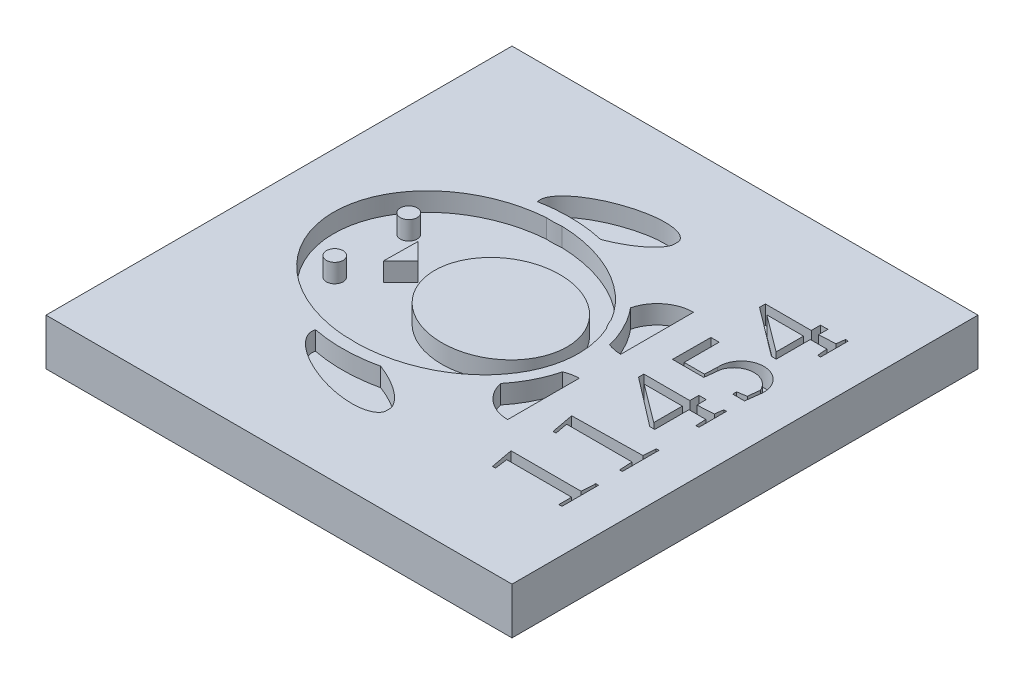
SolidWorks part; units mm, degrees
ref_plane "Front Plane" through (0, 0, 0) normal (0, 0, 1) x (1, 0, 0)
ref_plane "Top Plane" through (0, 0, 0) normal (0, 1, 0) x (1, 0, 0)
ref_plane "Right Plane" through (0, 0, 0) normal (1, 0, 0) x (0, 0, -1)
sketch "Sketch3" plane through (0, 0, 0) normal (0, 1, 0) x (1, 0, 0)
  line L1 (-31.75, 31.75) -> (31.75, 31.75)
  line L2 (-31.75, 31.75) -> (-31.75, -31.75)
  line L3 (-31.75, -31.75) -> (31.75, -31.75)
  line L4 (31.75, 31.75) -> (31.75, -31.75)
  line L5 (-31.75, 31.75) -> (31.75, -31.75) construction
  line L6 (-31.75, -31.75) -> (31.75, 31.75) construction
  point P0 (0, 0)
  dimension "D1" = 63.5
  dimension "D2" = 63.5
extrude "Boss-Extrude1" add sketch "Sketch3" along normal blind 6.35
sketch "Sketch4" plane through (0, 6.35, 0) normal (0, 1, 0) x (1, 0, 0)
  line L0 (-31.75, 0) -> (31.75, 0)
  line L1 (-31.75, 31.75) -> (-31.75, -31.75) construction
  line L2 (31.75, -31.75) -> (31.75, 31.75) construction
  line L3 (0, -31.75) -> (0, 31.75)
  line L4 (-31.75, -31.75) -> (31.75, -31.75) construction
  line L5 (31.75, 31.75) -> (-31.75, 31.75) construction
  line L6 (6.1011, -12.941) -> (6.1011, 12.941)
  line L7 (-11.491, -10.0831) -> (-11.491, 10.0831)
  line L8 (-11.491, 10.0831) -> (-11.491, 0)
  line L9 (-11.491, 0) -> (-11.491, -10.0831)
  line L10 (-11.491, 0) -> (-11.491, 10.0831)
  line L11 (-7.6663, -12.3498) -> (-7.3296, 12.4908)
  line L12 (-7.4679, 2.2902) -> (-5.1777, 0)
  line L13 (-5.1777, 0) -> (-7.5308, -2.3531)
  line L14 (19.6532, 0) -> (19.6532, 15.494)
  line L15 (19.6532, 15.494) -> (19.6532, -15.494)
  line L16 (19.6532, -15.494) -> (19.6532, 0)
  line L17 (19.6532, -15.494) -> (19.6532, 0)
  line L18 (19.6532, 0) -> (19.6532, -15.494)
  line L19 (3.1453, 17.5998) -> (3.1453, 13.6542)
  line L20 (3.1453, -17.5998) -> (3.1453, -13.6542)
  line L21 (10.3047, 20.0808) -> (10.3047, 10.9368)
  line L22 (10.3365, -20.0599) -> (10.3365, -10.9159)
  circle A0 centre (-11.491, -5.0416) radius 1.143
  circle A1 centre (-11.491, 5.0416) radius 1.143
  circle A2 centre (19.6532, 7.747) radius 4.9623
  circle A3 centre (19.6532, -7.747) radius 4.8737
  ellipse E0 centre (0, 0) end of major axis (16.6899, 0) minor radius 13.9033
  ellipse E1 centre (6.1011, 0) end of major axis (15.1321, 0) minor radius 8.0476
  ellipse E2 centre (0, 0) end of major axis (18.157, 0) minor radius 15.5025
  ellipse E3 centre (3.1453, 17.5998) end of major axis (-4.0142, 15.1189) minor radius 3.0241
  ellipse E4 centre (3.1453, -17.5998) end of major axis (10.3365, -20.0599) minor radius 2.9995
  point P51 (3.1453, -17.5998)
  point P60 (10.3365, -20.0599)
  dimension "D1" = 2.286
  dimension "D2" = 2.286
  dimension "D3" = 15.494
  dimension "D4" = 15.494
  dimension "D5" = 3.9457
  dimension "D6" = 9.144
  dimension "D7" = 9.144
  dimension "D8" = 3.9457
extrude "Cut-Extrude1" cut sketch "Sketch4" against normal blind 2.54
sketch "Sketch6" plane through (31.75, 0, 0) normal (1, 0, 0) x (0, 0, -1)
  line L1 (31.75, 6.35) -> (-31.75, 6.35)
  line L2 (31.75, 6.35) -> (31.75, 0)
  line L3 (31.75, 0) -> (-31.75, 0)
  line L4 (-31.75, 6.35) -> (-31.75, 0)
extrude "Boss-Extrude2" add sketch "Sketch6" along normal blind 7.62
sketch "Sketch7" plane through (-31.75, 0, 0) normal (-1, 0, 0) x (0, 0, 1)
  line L1 (-31.75, 0) -> (31.75, 0)
  line L2 (-31.75, 0) -> (-31.75, 6.35)
  line L3 (-31.75, 6.35) -> (31.75, 6.35)
  line L4 (31.75, 0) -> (31.75, 6.35)
extrude "Cut-Extrude2" cut sketch "Sketch7" against normal blind 7.62
sketch "Sketch12" plane through (0, 6.35, 0) normal (0, 1, 0) x (1, 0, 0)
  line L0 (33.5932, -31.75) -> (33.5932, 31.75)
  line L1 (-24.13, -31.75) -> (39.37, -31.75) construction
  line L2 (39.37, 31.75) -> (-24.13, 31.75) construction
  line L5 (33.5932, -19.1511) -> (33.1665, -19.1863)
  line L6 (33.1665, -19.1863) -> (33.1665, -17.423)
  line L7 (33.1665, -17.423) -> (24.3207, -17.423)
  line L8 (24.3207, -17.423) -> (24.5493, -19.1863)
  line L9 (24.5493, -19.1863) -> (24.1456, -19.1863)
  line L10 (24.1456, -19.1863) -> (23.5653, -16.0773)
  line L11 (23.5653, -16.0773) -> (33.1252, -16.0773)
  line L12 (33.1252, -16.0773) -> (33.2261, -14.1817)
  line L13 (33.2261, -14.1817) -> (33.5932, -14.1817)
  line L14 (33.5932, -14.1817) -> (33.5932, -19.1511)
  line L15 (23.5653, -7.8157) -> (24.1456, -10.935)
  line L16 (24.1456, -10.935) -> (24.5493, -10.935)
  line L17 (24.5493, -10.935) -> (24.2174, -9.1511)
  line L18 (24.2174, -9.1511) -> (33.1252, -9.1511)
  line L19 (33.1252, -9.1511) -> (33.2261, -10.935)
  line L20 (33.2261, -10.935) -> (33.5932, -10.935)
  line L21 (33.5932, -10.935) -> (33.5932, -5.9501)
  line L22 (33.5932, -5.9501) -> (33.2261, -5.9501)
  line L23 (33.2261, -5.9501) -> (33.1252, -7.6508)
  line L24 (33.1252, -7.6508) -> (23.5653, -7.8157)
  line L25 (23.5653, 1.2976) -> (30.1596, -3.7688)
  line L26 (30.1596, -3.7688) -> (30.8413, -3.7688)
  line L27 (30.8413, -3.7688) -> (30.8413, 0.8967)
  line L28 (30.8413, 0.8967) -> (33.1252, 0.8967)
  line L29 (33.1252, 0.8967) -> (33.2047, -0.5088)
  line L30 (33.2047, -0.5088) -> (33.5932, -0.5088)
  line L31 (33.5932, -0.5088) -> (33.5932, 3.2621)
  line L32 (33.5932, 3.2621) -> (33.2261, 3.2621)
  line L33 (33.2261, 3.2621) -> (33.0711, 2.1132)
  line L34 (33.0711, 2.1132) -> (30.8413, 1.987)
  line L35 (30.8413, 1.987) -> (30.8193, 3.2621)
  line L36 (30.8193, 3.2621) -> (29.8201, 3.2621)
  line L37 (29.8201, 3.2621) -> (29.8201, 2.028)
  line L38 (29.8201, 2.028) -> (23.5653, 2.028)
  line L39 (23.5653, 2.028) -> (23.5653, 1.2976)
  line L40 (24.5493, 0.8967) -> (29.8201, -3.1529)
  line L41 (29.8201, -3.1529) -> (29.8201, 0.8967)
  line L42 (24.5493, 0.8967) -> (29.8201, 0.8967)
  line L43 (33.872, 7.8761) -> (33.5932, 5.7123)
  line L44 (33.5932, 5.7123) -> (31.9822, 5.7123)
  line L45 (31.9822, 5.7123) -> (31.9822, 6.2447)
  line L46 (31.9822, 6.2447) -> (33.2261, 6.4512)
  line L47 (33.2261, 6.4512) -> (33.4138, 8.0633)
  line L48 (28.2811, 7.8007) -> (28.0379, 5.7123)
  line L49 (28.0379, 5.7123) -> (23.7767, 5.7123)
  line L50 (23.7767, 5.7123) -> (23.8069, 10.9197)
  line L51 (23.8069, 10.9197) -> (24.9322, 10.9197)
  line L52 (24.9322, 10.9197) -> (24.9322, 6.1458)
  line L53 (24.9322, 6.1458) -> (27.6984, 6.1458)
  line L54 (27.6984, 6.1458) -> (27.7736, 7.8761)
  line L55 (33.5932, 16.074) -> (33.5932, 19.8467)
  line L56 (33.5932, 19.8467) -> (33.2261, 19.8467)
  line L57 (33.2261, 19.8467) -> (33.0775, 18.6928)
  line L58 (33.0775, 18.6928) -> (30.8228, 18.5789)
  line L59 (30.8228, 18.5789) -> (30.8228, 19.8467)
  line L60 (30.8228, 19.8467) -> (29.8201, 19.8295)
  line L61 (29.8201, 19.8295) -> (29.8201, 18.5789)
  line L62 (29.8201, 18.5789) -> (23.5653, 18.5789)
  line L63 (23.5653, 18.5789) -> (23.5653, 17.7846)
  line L64 (23.5653, 17.7846) -> (30.1596, 12.808)
  line L65 (30.1596, 12.808) -> (30.8228, 12.808)
  line L66 (30.8228, 12.808) -> (30.8228, 17.4426)
  line L67 (30.8228, 17.4426) -> (33.0772, 17.4426)
  line L68 (33.0772, 17.4426) -> (33.1957, 16.074)
  line L69 (33.1957, 16.074) -> (33.5932, 16.074)
  line L70 (24.6589, 17.4426) -> (29.8201, 13.5475)
  line L71 (29.8201, 13.5475) -> (29.8201, 17.4426)
  line L72 (29.8201, 17.4426) -> (24.6589, 17.4426)
  arc A0 (33.872, 7.8761) -> (27.7736, 7.8761) centre (30.8228, 8.0633) ccw
  arc A1 (28.2811, 7.8007) -> (33.4138, 8.0633) centre (30.8966, 6.9705) cw
  text T0 "11454" font "Lucida Bright" height in points 36
extrude "Cut-Extrude4" cut sketch "Sketch12" against normal blind 2.54 contours L11 L12 L13 L14 L5 L6 L7 L8 L9 L10 | L18 L19 L20 L21 L22 L23 L24 L15 L16 L17 | L28 L29 L30 L31 L32 L33 L34 L35 L36 L37 L38 L39 L25 L26 L27 | A0 L54 L53 L52 L51 L50 L49 L48 A1 L47 L46 L45 L44 L43 | L67 L68 L69 L55 L56 L57 L58 L59 L60 L61 L62 L63 L64 L65 L66
sketch "Sketch13" plane through (0, 3.81, 0) normal (0, 1, 0) x (1, 0, 0)
  line L0 (29.9588, 0.8662) -> (29.9588, -3.0195)
  line L1 (29.9588, -3.0195) -> (24.7695, 0.8662)
  line L2 (24.7695, 0.8662) -> (29.9588, 0.8662)
  line L3 (29.9588, 17.388) -> (29.9588, 13.6504)
  line L4 (29.9588, 13.6504) -> (24.9672, 17.388)
  line L5 (24.9672, 17.388) -> (29.9588, 17.388)
extrude "Boss-Extrude3" add sketch "Sketch13" along normal blind 2.54
